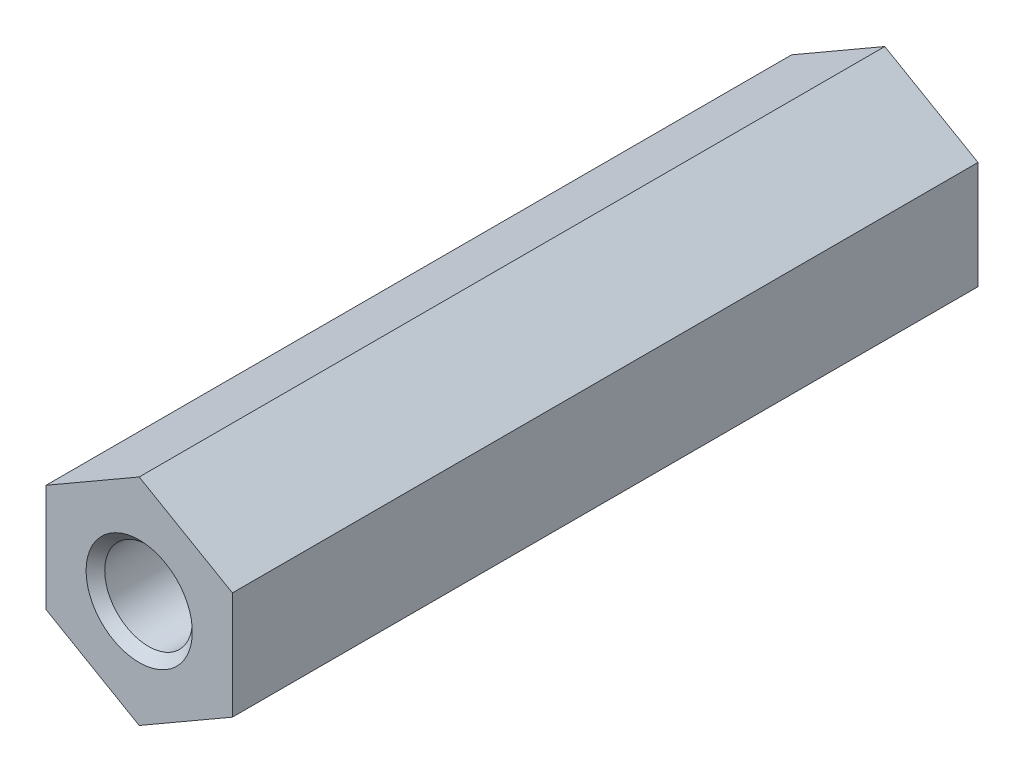
SolidWorks part; units mm, degrees
ref_plane "Front Plane" through (0, 0, 0) normal (0, 0, 1) x (1, 0, 0)
ref_plane "Top Plane" through (0, 0, 0) normal (0, 1, 0) x (1, 0, 0)
ref_plane "Right Plane" through (0, 0, 0) normal (1, 0, 0) x (0, 0, -1)
ref_plane "Plane1" through (0, 0, 0) normal (0, 0, -1) x (-1, 0, 0)
sketch "Sketch1" plane through (0, 0, 0) normal (0, 0, -1) x (-1, 0, 0)
  line L0 (-5, 2.8868) -> (-5, -2.8868)
  line L1 (-5, -2.8868) -> (0, -5.7735)
  line L2 (0, -5.7735) -> (5, -2.8868)
  line L3 (5, -2.8868) -> (5, 2.8868)
  line L4 (5, 2.8868) -> (0, 5.7735)
  line L5 (0, 5.7735) -> (-5, 2.8868)
  circle A0 centre (0, 0) radius 2.35
extrude "Boss-Extrude1" add sketch "Sketch1" against normal blind 40
chamfer "Chamfer4" distance 0.5 angle 45 2 edges at (2.35, 0, 0) (2.35, 0, 40)
